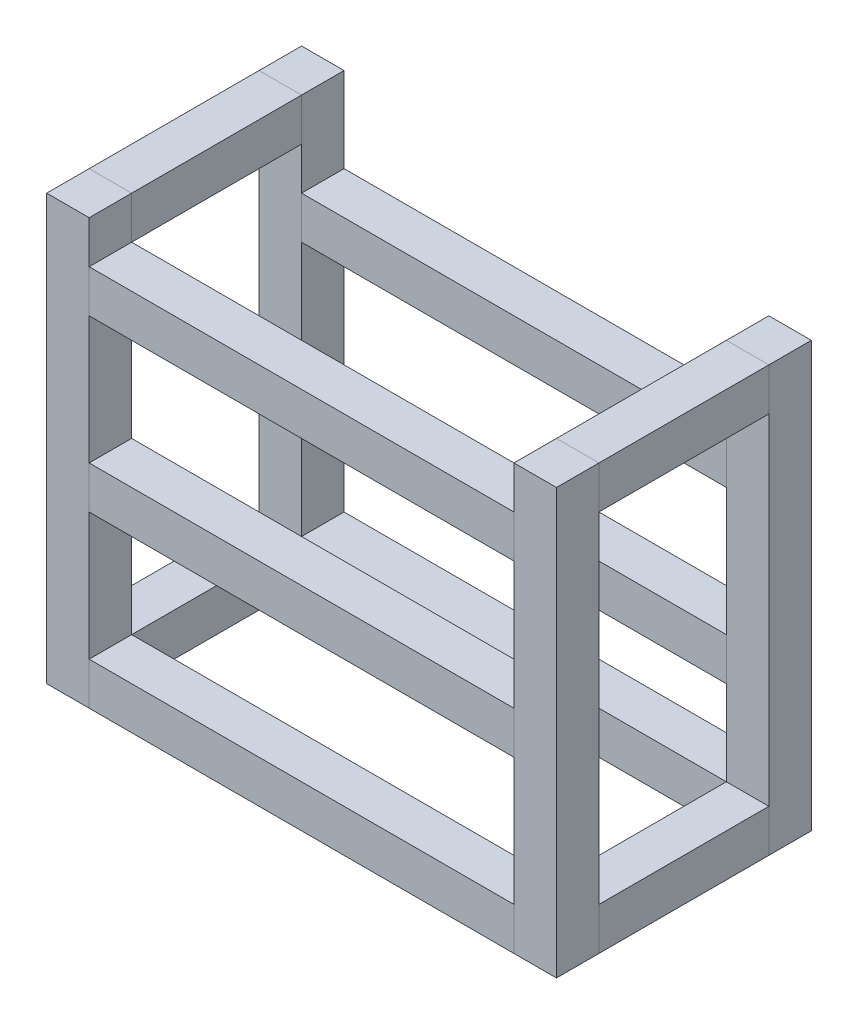
SolidWorks part; units mm, degrees
material "6061 Alloy"
ref_plane "Front Plane" through (0, 0, 0) normal (0, 0, 1) x (1, 0, 0)
ref_plane "Top Plane" through (0, 0, 0) normal (0, 1, 0) x (1, 0, 0)
ref_plane "Right Plane" through (0, 0, 0) normal (1, 0, 0) x (0, 0, -1)
sketch "Sketch1" plane through (0, 0, 0) normal (0, 1, 0) x (1, 0, 0)
  line L1 (-152.4, -76.2) -> (152.4, -76.2)
  line L2 (-152.4, -76.2) -> (-152.4, 76.2)
  line L3 (-152.4, 76.2) -> (152.4, 76.2)
  line L4 (152.4, -76.2) -> (152.4, 76.2)
  line L5 (-152.4, -76.2) -> (152.4, 76.2) construction
  line L6 (-152.4, 76.2) -> (152.4, -76.2) construction
  line L7 (-152.4, 76.2) -> (-127, 76.2)
  line L8 (-152.4, 76.2) -> (-152.4, 50.8)
  line L9 (-152.4, 50.8) -> (-127, 50.8)
  line L10 (-127, 76.2) -> (-127, 50.8)
  line L11 (152.4, 76.2) -> (127, 76.2)
  line L12 (152.4, 76.2) -> (152.4, 50.8)
  line L13 (152.4, 50.8) -> (127, 50.8)
  line L14 (127, 76.2) -> (127, 50.8)
  line L15 (-152.4, -76.2) -> (-127, -76.2)
  line L16 (-152.4, -76.2) -> (-152.4, -50.8)
  line L17 (-152.4, -50.8) -> (-127, -50.8)
  line L18 (-127, -76.2) -> (-127, -50.8)
  line L19 (152.4, -76.2) -> (127, -76.2)
  line L20 (152.4, -76.2) -> (152.4, -50.8)
  line L21 (152.4, -50.8) -> (127, -50.8)
  line L22 (127, -76.2) -> (127, -50.8)
  point P0 (0, 0)
  dimension "D1" = 25.4
  dimension "D2" = 254
  dimension "D3" = 101.6
extrude "Boss-Extrude1" add sketch "Sketch1" along normal blind 254 contours L10 L3 L2 L9 | L1 L18 L17 L2 | L22 L1 L4 L21 | L3 L14 L13 L4
sketch "Sketch2" plane through (0, 0, 0) normal (1, 0, 0) x (0, 0, -1)
  line L0 (-76.2, 254) -> (-76.2, 0) construction
  line L1 (-76.2, 228.6) -> (-50.8, 228.6)
  line L2 (-76.2, 228.6) -> (-76.2, 203.2)
  line L3 (-76.2, 203.2) -> (-50.8, 203.2)
  line L4 (-50.8, 228.6) -> (-50.8, 203.2)
  line L5 (50.8, 203.2) -> (76.2, 203.2)
  line L6 (50.8, 203.2) -> (50.8, 177.8)
  line L7 (50.8, 177.8) -> (76.2, 177.8)
  line L8 (76.2, 203.2) -> (76.2, 177.8)
  line L9 (-76.2, 25.4) -> (-50.8, 25.4)
  line L10 (-76.2, 25.4) -> (-76.2, 0)
  line L11 (-76.2, 0) -> (-50.8, 0)
  line L12 (-50.8, 25.4) -> (-50.8, 0)
  line L13 (50.8, 25.4) -> (76.2, 25.4)
  line L14 (50.8, 25.4) -> (50.8, 0)
  line L15 (50.8, 0) -> (76.2, 0)
  line L16 (76.2, 25.4) -> (76.2, 0)
  line L17 (-76.2, 127) -> (-50.8, 127)
  line L18 (-76.2, 127) -> (-76.2, 101.6)
  line L19 (-76.2, 101.6) -> (-50.8, 101.6)
  line L20 (-50.8, 127) -> (-50.8, 101.6)
  line L21 (50.8, 101.6) -> (76.2, 101.6)
  line L22 (50.8, 101.6) -> (50.8, 76.2)
  line L23 (50.8, 76.2) -> (76.2, 76.2)
  line L24 (76.2, 101.6) -> (76.2, 76.2)
  line L25 (76.2, 254) -> (76.2, 0) construction
  line L26 (-76.2, 0) -> (-50.8, 0) construction
  line L27 (76.2, 0) -> (50.8, 0) construction
  point P28 (0, 0)
  point P33 (0, 0)
  point P34 (0, 0)
  point P35 (0, 0)
  dimension "D1" = 25.4
  dimension "D2" = 228.6
  dimension "D3" = 127
  dimension "D4" = 101.6
  dimension "D5" = 203.2
extrude "Boss-Extrude2" add sketch "Sketch2" along normal up to next (127 mm away) and the other way up to next (127 mm away) separate body
sketch "Sketch3" plane through (0, 0, 0) normal (0, 0, 1) x (1, 0, 0)
  line L1 (-152.4, 254) -> (-127, 254)
  line L2 (-152.4, 254) -> (-152.4, 228.6)
  line L3 (-152.4, 228.6) -> (-127, 228.6)
  line L4 (-127, 254) -> (-127, 228.6)
  line L5 (-152.4, 25.4) -> (-127, 25.4)
  line L6 (-152.4, 25.4) -> (-152.4, 0)
  line L7 (-152.4, 0) -> (-127, 0)
  line L8 (-127, 25.4) -> (-127, 0)
  line L9 (127, 254) -> (152.4, 254)
  line L10 (127, 254) -> (127, 228.6)
  line L11 (127, 228.6) -> (152.4, 228.6)
  line L12 (152.4, 254) -> (152.4, 228.6)
  line L13 (127, 25.4) -> (152.4, 25.4)
  line L14 (127, 25.4) -> (127, 0)
  line L15 (127, 0) -> (152.4, 0)
  line L16 (152.4, 25.4) -> (152.4, 0)
  point P16 (0, 0)
  point P17 (0, 0)
  point P20 (0, 0)
  point P22 (0, 0)
  dimension "D1" = 25.4
extrude "Boss-Extrude3" add sketch "Sketch3" along normal up to next (50.8 mm away) and the other way up to next (50.8 mm away) separate body
